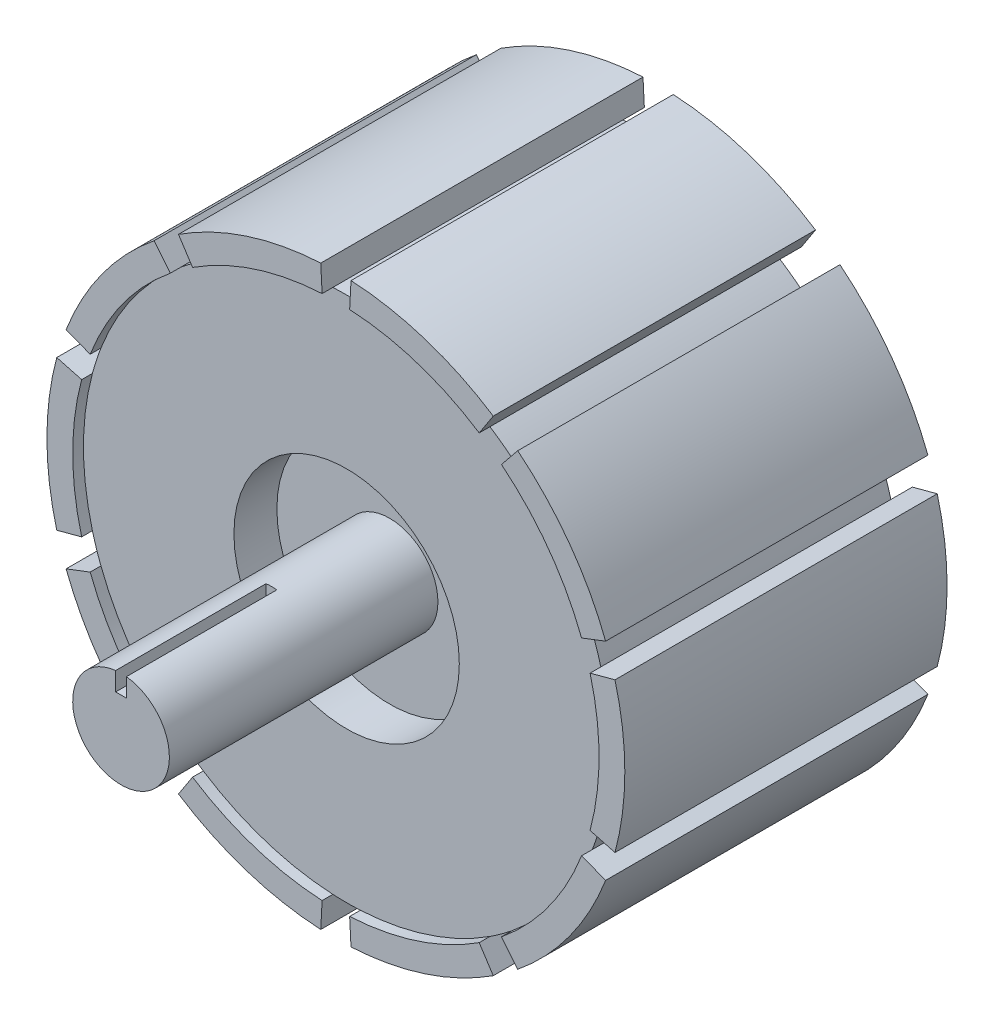
SolidWorks part; units mm, degrees
ref_plane "Front Plane" through (0, 0, 0) normal (0, 0, 1) x (1, 0, 0)
ref_plane "Top Plane" through (0, 0, 0) normal (0, 1, 0) x (1, 0, 0)
ref_plane "Right Plane" through (0, 0, 0) normal (1, 0, 0) x (0, 0, -1)
sketch "Sketch1" plane through (0, 0, 0) normal (0, 0, 1) x (1, 0, 0)
  circle A0 centre (0, 0) radius 24.5
  dimension "D1" = 49
extrude "Boss-Extrude1" add sketch "Sketch1" along normal blind 30
sketch "Sketch2" plane through (0, 0, 30) normal (0, 0, 1) x (1, 0, 0)
  circle A0 centre (0, 0) radius 10.4916
extrude "Cut-Extrude1" cut sketch "Sketch2" against normal blind 5
sketch "Sketch4" plane through (0, 0, 25) normal (0, 0, 1) x (1, 0, 0)
  circle A0 centre (0, 0) radius 4.5
  dimension "D1" = 9
sketch "Sketch5" plane through (0, 0, 0) normal (0, 0, -1) x (-1, 0, 0)
  line L0 (-22.8727, 8.78) -> (-25.1133, 9.6401)
  line L1 (-15.4183, 19.0401) -> (-16.9287, 20.9052)
  line L2 (-13.3437, 20.5474) -> (-14.6508, 22.5602)
  line L3 (-1.2822, 24.4664) -> (-1.4078, 26.8631)
  line L4 (1.2822, 24.4664) -> (1.4078, 26.8631)
  line L5 (13.3437, 20.5474) -> (14.6508, 22.5602)
  line L6 (15.4183, 19.0401) -> (16.9287, 20.9052)
  line L7 (22.8727, 8.78) -> (25.1133, 9.6401)
  line L8 (23.6652, 6.3411) -> (25.9834, 6.9622)
  line L9 (23.6652, -6.3411) -> (25.9834, -6.9622)
  line L10 (22.8727, -8.78) -> (25.1133, -9.6401)
  line L11 (15.4183, -19.0401) -> (16.9287, -20.9052)
  line L12 (13.3437, -20.5474) -> (14.6508, -22.5602)
  line L13 (1.2822, -24.4664) -> (1.4078, -26.8631)
  line L14 (-1.2822, -24.4664) -> (-1.4078, -26.8631)
  line L15 (-13.3437, -20.5474) -> (-14.6508, -22.5602)
  line L16 (-15.4183, -19.0401) -> (-16.9287, -20.9052)
  line L17 (-22.8727, -8.78) -> (-25.1133, -9.6401)
  line L18 (-23.6652, -6.3411) -> (-25.9834, -6.9622)
  line L19 (-23.6652, 6.3411) -> (-25.9834, 6.9622)
  arc A0 (-16.9287, 20.9052) -> (-25.1133, 9.6401) centre (0, 0) ccw
  arc A2 (-1.4078, 26.8631) -> (-14.6508, 22.5602) centre (0, 0) ccw
  arc A3 (14.6508, 22.5602) -> (1.4078, 26.8631) centre (0, 0) ccw
  circle A4 centre (0, 0) radius 24.5 construction
  arc A5 (25.1133, 9.6401) -> (16.9287, 20.9052) centre (0, 0) ccw
  arc A6 (25.9834, -6.9622) -> (25.9834, 6.9622) centre (0, 0) ccw
  arc A7 (16.9287, -20.9052) -> (25.1133, -9.6401) centre (0, 0) ccw
  arc A8 (1.4078, -26.8631) -> (14.6508, -22.5602) centre (0, 0) ccw
  arc A9 (-14.6508, -22.5602) -> (-1.4078, -26.8631) centre (0, 0) ccw
  arc A10 (-25.1133, -9.6401) -> (-16.9287, -20.9052) centre (0, 0) ccw
  arc A11 (-25.9834, 6.9622) -> (-25.9834, -6.9622) centre (0, 0) ccw
  circle A12 centre (0, 0) radius 24.5
  point P45 (0, 0)
  circle M5 centre (0, 0) radius 24.5
  dimension "D1" = 10
extrude "Boss-Extrude3" add sketch "Sketch5" against normal blind 30 contours L15 A9 L14 M5 | L13 A8 L12 M5 | L11 A7 L10 M5 | L9 A6 L8 M5 | L7 A5 L6 M5 | L5 A3 L4 M5 | L3 A2 L2 M5 | L1 A0 L0 M5 | L19 A11 L18 M5 | L17 A10 L16 M5
sketch "Sketch6" plane through (0, 0, 0) normal (0, 0, -1) x (-1, 0, 0)
  circle A0 centre (0, 0) radius 24.5
extrude "Cut-Extrude2" cut sketch "Sketch6" against normal blind 2
sketch "Sketch7" plane through (0, 0, 30) normal (0, 0, 1) x (1, 0, 0)
  circle A0 centre (0, 0) radius 24.5
extrude "Cut-Extrude4" cut sketch "Sketch7" against normal blind 1
extrude "Boss-Extrude4" add sketch "Sketch4" along normal blind 25 contours A0
sketch "Sketch8" plane through (0, 0, 50) normal (0, 0, 1) x (1, 0, 0)
  line L0 (-0.5, 2.7422) -> (0.5, 2.7422)
  line L1 (-0.5, 2.7422) -> (-0.5, 4.4721)
  line L2 (0.5, 2.7422) -> (0.5, 4.4721)
  arc A0 (0.5, 4.4721) -> (-0.5, 4.4721) centre (0, 0) ccw
  dimension "D1" = 0.5
  dimension "D2" = 1
  dimension "D3" = 1.7299
extrude "Cut-Extrude5" cut sketch "Sketch8" against normal blind 14 contours L0 L2 A0 L1
